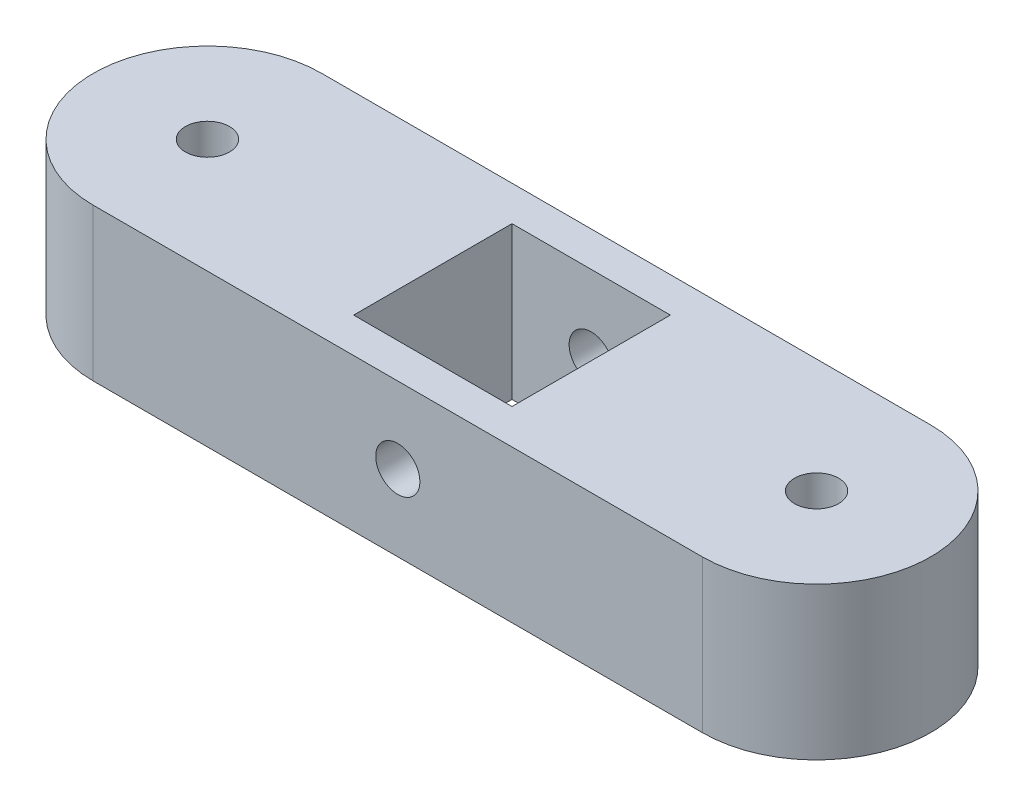
SolidWorks part; units mm, degrees
material "ABS"
ref_plane "Front Plane" through (0, 0, 0) normal (0, 0, 1) x (1, 0, 0)
ref_plane "Top Plane" through (0, 0, 0) normal (0, 1, 0) x (1, 0, 0)
ref_plane "Right Plane" through (0, 0, 0) normal (1, 0, 0) x (0, 0, -1)
sketch "Sketch1" plane through (0, 0, 0) normal (0, 1, 0) x (1, 0, 0)
  line L0 (-50.8, 0) -> (50.8, 0) construction
  line L1 (-50.8, 19.05) -> (50.8, 19.05)
  line L2 (-50.8, -19.05) -> (50.8, -19.05)
  line L3 (0, 31.9992) -> (0, -34.998) construction
  line L4 (-13.208, 13.208) -> (-13.208, -13.208)
  line L5 (-12.7, 12.7) -> (12.7, 12.7) construction
  line L6 (-12.7, 12.7) -> (-12.7, -12.7) construction
  line L7 (-12.7, -12.7) -> (12.7, -12.7) construction
  line L8 (12.7, 12.7) -> (12.7, -12.7) construction
  line L9 (-12.7, 12.7) -> (12.7, -12.7) construction
  line L10 (-12.7, -12.7) -> (12.7, 12.7) construction
  line L11 (-13.208, -13.208) -> (13.208, -13.208)
  line L12 (13.208, 13.208) -> (13.208, -13.208)
  line L13 (-13.208, 13.208) -> (13.208, 13.208)
  arc A0 (-50.8, 19.05) -> (-50.8, -19.05) centre (-50.8, 0) ccw
  arc A1 (50.8, -19.05) -> (50.8, 19.05) centre (50.8, 0) ccw
  circle A2 centre (-50.8, 0) radius 3.175 construction
  circle A3 centre (-50.8, 0) radius 3.683
  circle A4 centre (50.8, 0) radius 3.683
  point P3 (0, 0)
  point P13 (0, 0)
  dimension "D3" = 6.35
  dimension "D4" = 0.508
  dimension "D1" = 101.6
  dimension "D2" = 38.1
  dimension "D5" = 25.4
  dimension "D6" = 25.4
  dimension "D7" = 0.508
extrude "Boss-Extrude1" add sketch "Sketch1" along normal blind 25.4
sketch "Sketch2" plane through (0, 0, 19.05) normal (0, 0, 1) x (1, 0, 0)
  line L0 (0, 0) -> (0, 25.4) construction
  line L1 (-50.8, 0) -> (50.8, 0) construction
  line L2 (-50.8, 25.4) -> (50.8, 25.4) construction
  circle A0 centre (0, 12.7) radius 3.683
  dimension "D1" = 7.366
extrude "Cut-Extrude1" cut sketch "Sketch2" against normal through all
